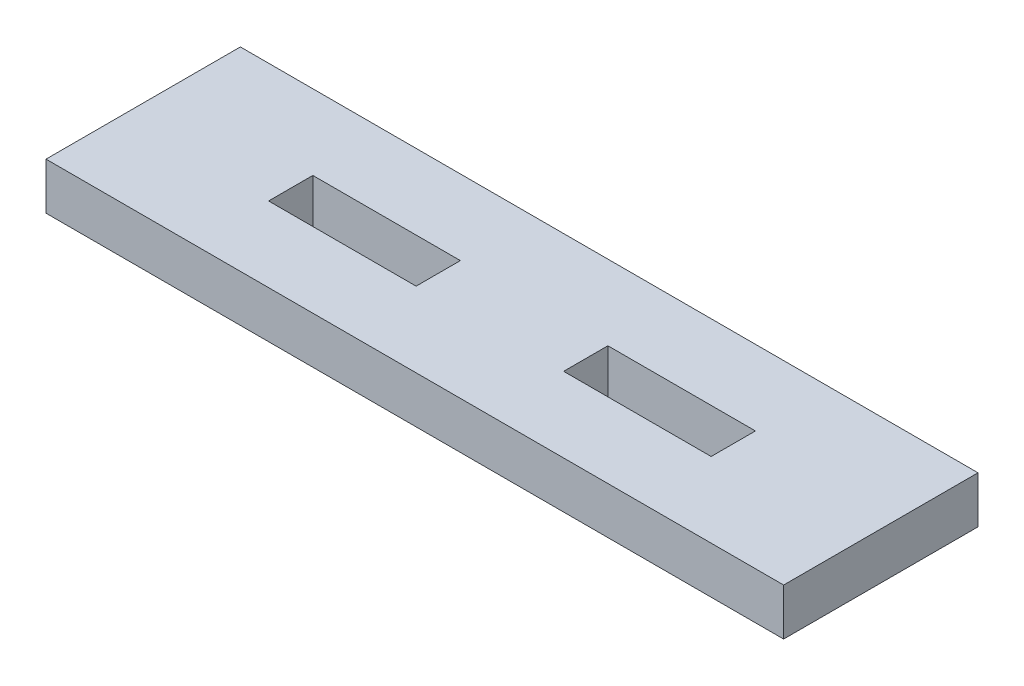
SolidWorks part; units mm, degrees
ref_plane "Front Plane" through (0, 0, 0) normal (0, 0, 1) x (1, 0, 0)
ref_plane "Top Plane" through (0, 0, 0) normal (0, 1, 0) x (1, 0, 0)
ref_plane "Right Plane" through (0, 0, 0) normal (1, 0, 0) x (0, 0, -1)
sketch "Sketch1" plane through (0, 0, 0) normal (0, 1, 0) x (1, 0, 0)
  line L0 (0, 6.5875) -> (8.175, 6.5875) construction
  line L1 (0, 0) -> (50, 0)
  line L2 (0, 0) -> (0, 13.175)
  line L3 (0, 13.175) -> (50, 13.175)
  line L4 (50, 0) -> (50, 13.175)
  line L5 (25, 13.175) -> (25, 0) construction
  line L6 (0, 6.5875) -> (50, 6.5875) construction
  line L7 (8.175, 6.5875) -> (15, 6.5875) construction
  line L8 (30, 5.0875) -> (40, 5.0875)
  line L9 (10, 5.0875) -> (20, 5.0875)
  line L10 (10, 5.0875) -> (10, 8.0875)
  line L11 (10, 8.0875) -> (20, 8.0875)
  line L12 (20, 5.0875) -> (20, 8.0875)
  line L13 (10, 5.0875) -> (20, 8.0875) construction
  line L14 (10, 8.0875) -> (20, 5.0875) construction
  line L15 (30, 5.0875) -> (30, 8.0875)
  line L16 (30, 8.0875) -> (40, 8.0875)
  line L17 (40, 5.0875) -> (40, 8.0875)
  line L18 (28.175, 6.5875) -> (35, 6.5875) construction
  line L19 (30, 5.0875) -> (40, 8.0875) construction
  line L20 (30, 8.0875) -> (40, 5.0875) construction
  point P28 (25, 6.5875)
  dimension "D1" = 2
  dimension "D2" = 13.175
  dimension "D3" = 50
  dimension "D4" = 10
  dimension "D5" = 10
  dimension "D6" = 3
  dimension "D7" = 10
extrude "Boss-Extrude1" add sketch "Sketch1" along normal blind 3.175
